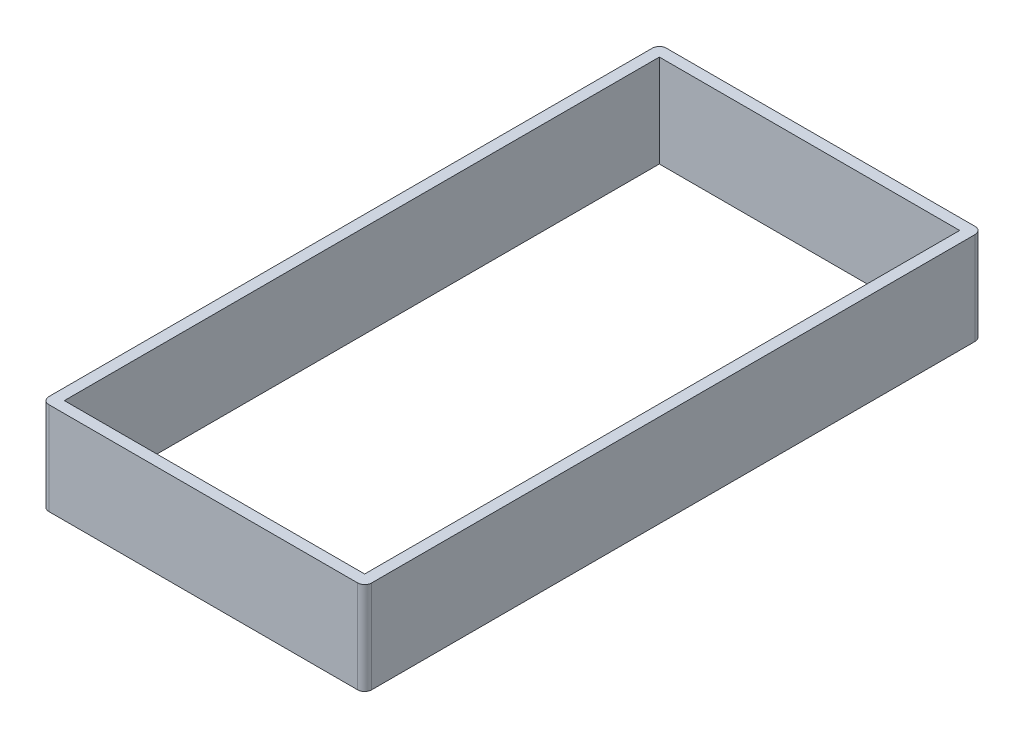
SolidWorks part; units mm, degrees
material "PC High Viscosity"
ref_plane "Front Plane" through (0, 0, 0) normal (0, 0, 1) x (1, 0, 0)
ref_plane "Top Plane" through (0, 0, 0) normal (0, 1, 0) x (1, 0, 0)
ref_plane "Right Plane" through (0, 0, 0) normal (1, 0, 0) x (0, 0, -1)
sketch "BaseS" plane through (0, 0, 0) normal (0, 1, 0) x (1, 0, 0)
  line L1 (-11.5, 22) -> (11.5, 22)
  line L2 (-11.5, 22) -> (-11.5, -22)
  line L3 (-11.5, -22) -> (11.5, -22)
  line L4 (11.5, 22) -> (11.5, -22)
  line L5 (-11.5, 22) -> (11.5, -22) construction
  line L6 (-11.5, -22) -> (11.5, 22) construction
  point P0 (0, 0)
  dimension "D1" = 23
  dimension "D2" = 44
extrude "BASE" add sketch "BaseS" along normal mid plane 6.6
fillet "BASE F" radius 0.5 4 edges at (-11.5, 0, -22) (11.5, 0, -22) (11.5, 0, 22) (-11.5, 0, 22)
sketch "PocketS" plane through (0, 3.3, 0) normal (0, 1, 0) x (1, 0, 0)
  line L0 (10.7, 21.2) -> (-10.7, 21.2)
  line L1 (-10.7, 21.2) -> (-10.7, -21.2)
  line L2 (-10.7, -21.2) -> (10.7, -21.2)
  line L3 (10.7, -21.2) -> (10.7, 21.2)
  line L4 (11, 22) -> (-11, 22)
  line L5 (-11.5, 21.5) -> (-11.5, -21.5)
  line L6 (-11, -22) -> (11, -22)
  line L7 (11.5, -21.5) -> (11.5, 21.5)
  line L8 (11, 22) -> (-11, 22) construction
  line L9 (-11.5, 21.5) -> (-11.5, -21.5) construction
  line L10 (-11, -22) -> (11, -22) construction
  line L11 (11.5, -21.5) -> (11.5, 21.5) construction
  arc A0 (-10.7, 21.2) -> (-10.7, 21.2) centre (-10.7, 21.2) ccw
  arc A1 (-10.7, -21.2) -> (-10.7, -21.2) centre (-10.7, -21.2) ccw
  arc A2 (10.7, -21.2) -> (10.7, -21.2) centre (10.7, -21.2) ccw
  arc A3 (10.7, 21.2) -> (10.7, 21.2) centre (10.7, 21.2) ccw
  arc A4 (-11, 22) -> (-11.5, 21.5) centre (-11, 21.5) ccw
  arc A5 (-11.5, -21.5) -> (-11, -22) centre (-11, -21.5) ccw
  arc A6 (11, -22) -> (11.5, -21.5) centre (11, -21.5) ccw
  arc A7 (11.5, 21.5) -> (11, 22) centre (11, 21.5) ccw
  arc A8 (-11, 22) -> (-11.5, 21.5) centre (-11, 21.5) ccw construction
  arc A9 (-11.5, -21.5) -> (-11, -22) centre (-11, -21.5) ccw construction
  arc A10 (11, -22) -> (11.5, -21.5) centre (11, -21.5) ccw construction
  arc A11 (11.5, 21.5) -> (11, 22) centre (11, 21.5) ccw construction
  dimension "D1" = 0
  dimension "D2" = 0.8
extrude "Cut-Extrude3" cut sketch "PocketS" against normal through all
